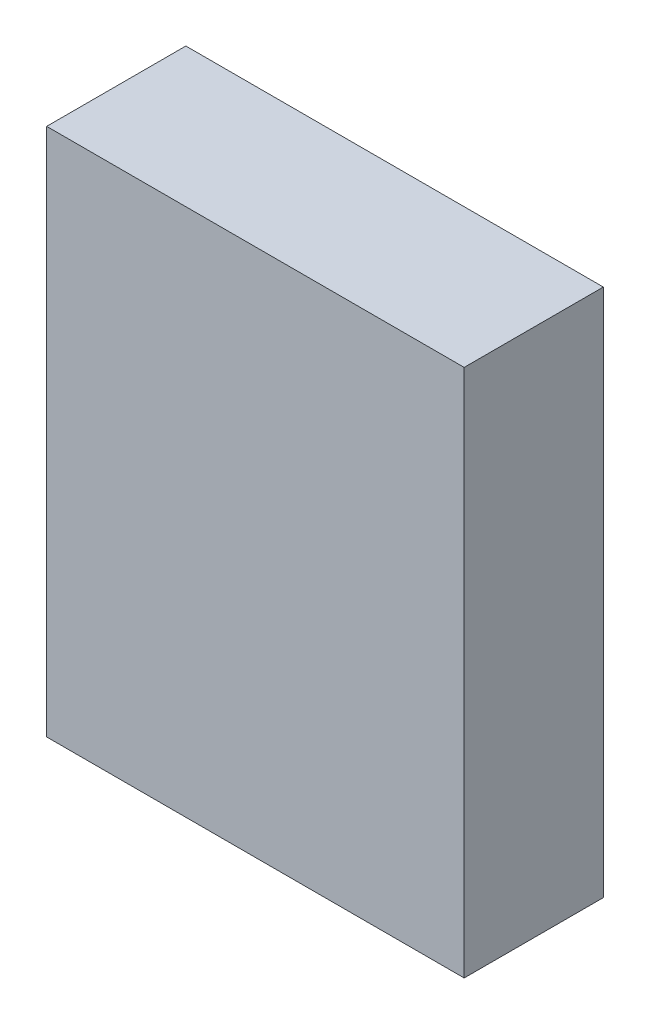
SolidWorks part; units mm, degrees
ref_plane "Ebene vorne" through (0, 0, 0) normal (0, 0, 1) x (1, 0, 0)
ref_plane "Ebene oben" through (0, 0, 0) normal (0, 1, 0) x (1, 0, 0)
ref_plane "Ebene rechts" through (0, 0, 0) normal (1, 0, 0) x (0, 0, -1)
sketch "Skizze1" plane through (0, 0, 0) normal (0, 0, 1) x (1, 0, 0)
  line L1 (-7.5, -9.5) -> (7.5, -9.5)
  line L2 (-7.5, -9.5) -> (-7.5, 9.5)
  line L3 (-7.5, 9.5) -> (7.5, 9.5)
  line L4 (7.5, -9.5) -> (7.5, 9.5)
  line L5 (-7.5, -9.5) -> (7.5, 9.5) construction
  line L6 (-7.5, 9.5) -> (7.5, -9.5) construction
  point P0 (0, 0)
  dimension "D1" = 15
  dimension "D2" = 19
extrude "Aufsatz-Linear austragen1" add sketch "Skizze1" along normal blind 5
